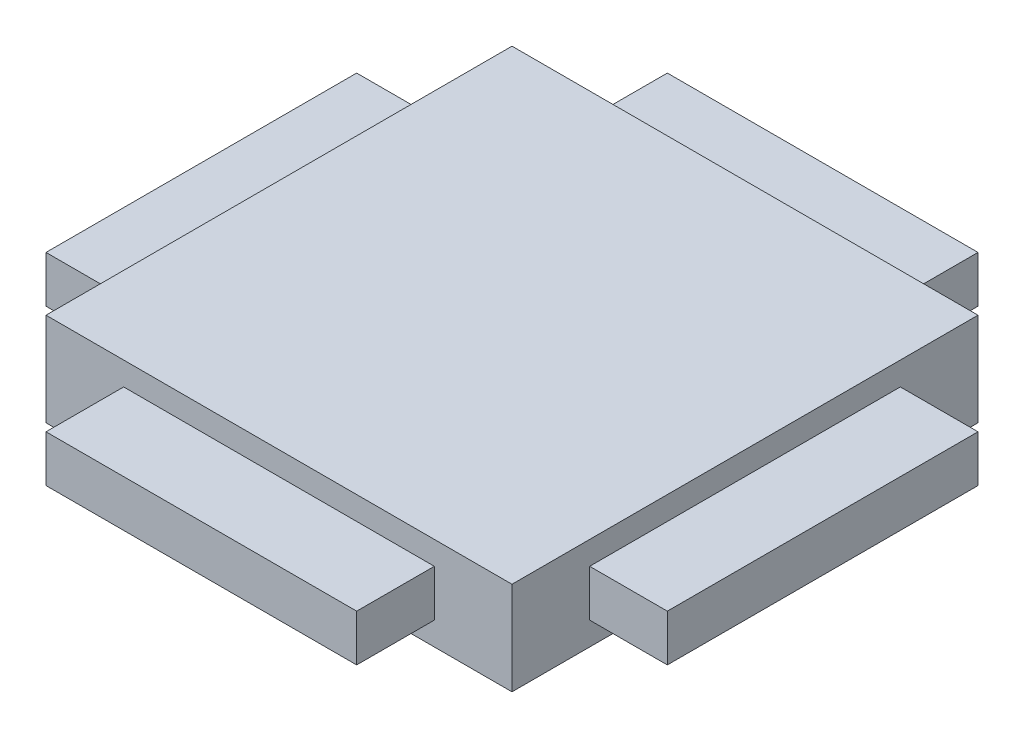
SolidWorks part; units mm, degrees
ref_plane "Front Plane" through (0, 0, 0) normal (0, 0, 1) x (1, 0, 0)
ref_plane "Top Plane" through (0, 0, 0) normal (0, 1, 0) x (1, 0, 0)
ref_plane "Right Plane" through (0, 0, 0) normal (1, 0, 0) x (0, 0, -1)
sketch "Sketch1" plane through (0, 0, 0) normal (0, 1, 0) x (1, 0, 0)
  line L1 (10, -9.7763) -> (-10, -9.7763)
  line L2 (10, -9.7763) -> (10, 10.2237)
  line L3 (10, 10.2237) -> (-10, 10.2237)
  line L4 (-10, -9.7763) -> (-10, 10.2237)
  line L5 (7.5, -7.5) -> (-7.5, -7.5)
  line L6 (7.5, -7.5) -> (7.5, 7.5)
  line L7 (7.5, 7.5) -> (-7.5, 7.5)
  line L8 (-7.5, -7.5) -> (-7.5, 7.5)
  line L9 (0, 7.5) -> (0, -7.5) construction
  line L10 (7.5, 0) -> (-7.5, 0) construction
  point P0 (0, 0)
  point P4 (0, 0)
  dimension "D1" = 20
  dimension "D2" = 20
  dimension "D3" = 15
  dimension "D4" = 15
extrude "Boss-Extrude2" add sketch "Sketch1" along normal blind 3 contours L8 L5 L6 L7
ref_plane "Plane1" through (0, 1.5, 0) normal (0, 1, 0) x (1, 0, 0)
sketch "Sketch4" plane through (0, 1.5, 0) normal (0, 1, 0) x (1, 0, 0)
  line L1 (10, -5) -> (-10, -5)
  line L2 (10, -5) -> (10, 5)
  line L3 (10, 5) -> (-10, 5)
  line L4 (-7.5, 7.5) -> (-7.5, -7.5)
  line L5 (-7.5, -7.5) -> (7.5, -7.5)
  line L6 (7.5, -7.5) -> (7.5, 7.5)
  line L7 (7.5, 7.5) -> (-7.5, 7.5)
  line L8 (-7.5, 7.5) -> (-7.5, -7.5)
  line L9 (-7.5, -7.5) -> (7.5, -7.5)
  line L10 (7.5, -7.5) -> (7.5, 7.5)
  line L11 (7.5, 7.5) -> (-7.5, 7.5)
  line L12 (-10, -5) -> (-10, 5)
  line L13 (0, 5) -> (0, -5) construction
  line L14 (10, 0) -> (-10, 0) construction
  line L15 (5, -10) -> (-5, -10)
  line L16 (5, -10) -> (5, 10)
  line L17 (5, 10) -> (-5, 10)
  line L18 (-5, -10) -> (-5, 10)
  line L19 (0, 10) -> (0, -10) construction
  line L20 (5, 0) -> (-5, 0) construction
  point P2 (0, 0)
  point P8 (0, 0)
  dimension "D2" = 10
  dimension "D3" = 20
  dimension "D4" = 10
  dimension "D5" = 20
  dimension "D1" = 0
extrude "Boss-Extrude3" add sketch "Sketch4" along normal blind 0.75 and the other way blind 0.75 contours L12 L1 L8 L3 | L18 L15 L16 L9 | L10 L1 L2 L3 | L18 L11 L16 L17
